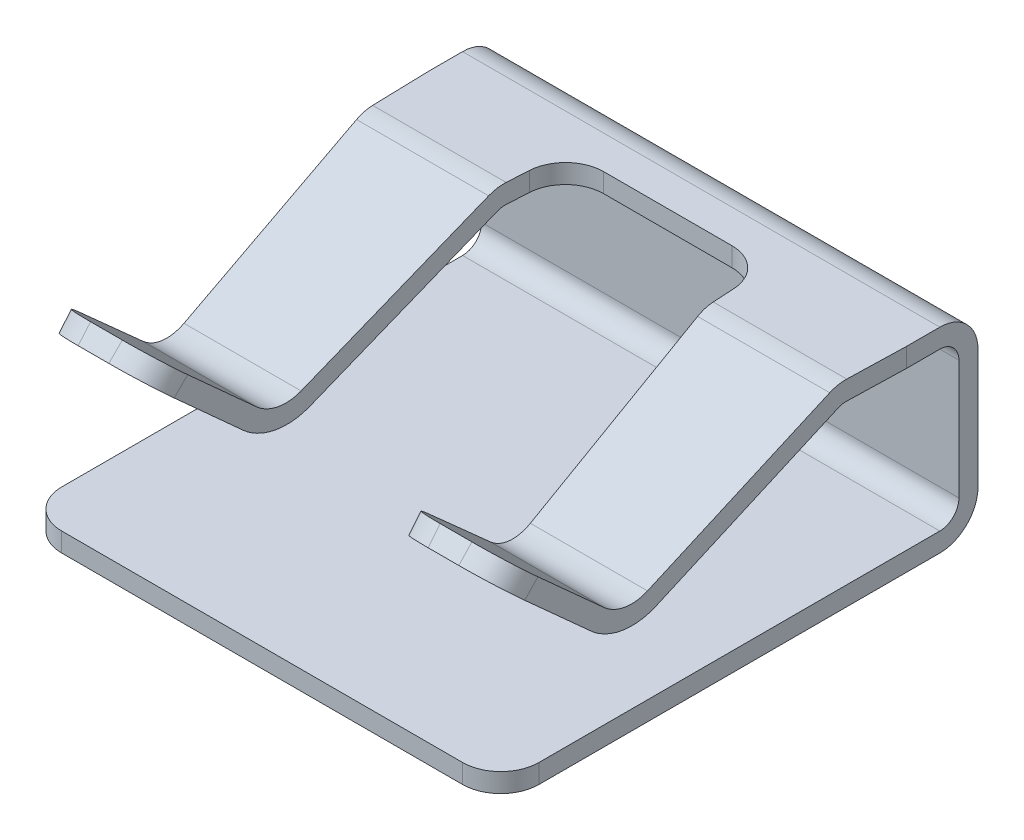
SolidWorks part; units mm, degrees
ref_plane "Front Plane" through (0, 0, 0) normal (0, 0, 1) x (1, 0, 0)
ref_plane "Top Plane" through (0, 0, 0) normal (0, 1, 0) x (1, 0, 0)
ref_plane "Right Plane" through (0, 0, 0) normal (1, 0, 0) x (0, 0, -1)
sketch "Sketch1" plane through (0, 0, 0) normal (1, 0, 0) x (0, 0, -1)
  line L0 (0, 0.4) -> (0, 1.65)
  line L1 (-0.4, 2.05) -> (-1.3588, 2.05)
  line L2 (-1.5322, 2.0105) -> (-3.3908, 1.1162)
  line L3 (-3.8317, 1.1793) -> (-4.8, 2.05)
  line L4 (-0.4, 0) -> (-5, 0)
  line L5 (-0.4, 0.2) -> (-5, 0.2)
  line L6 (-0.2, 0.4) -> (-0.2, 1.65)
  line L7 (-0.4, 1.85) -> (-1.3588, 1.85)
  line L8 (-1.4455, 1.8302) -> (-3.3041, 0.936)
  line L9 (-3.9655, 1.0305) -> (-4.9337, 1.9013)
  line L10 (-4.9337, 1.9013) -> (-4.8, 2.05)
  line L11 (-5, 0.2) -> (-5, 0)
  arc A0 (0, 0.4) -> (-0.4, 0) centre (-0.4, 0.4) cw
  arc A1 (0, 1.65) -> (-0.4, 2.05) centre (-0.4, 1.65) ccw
  arc A2 (-3.3908, 1.1162) -> (-3.8317, 1.1793) centre (-3.5643, 1.4767) cw
  arc A3 (-1.3588, 2.05) -> (-1.5322, 2.0105) centre (-1.3588, 1.65) ccw
  arc A4 (-0.2, 0.4) -> (-0.4, 0.2) centre (-0.4, 0.4) cw
  arc A5 (-0.2, 1.65) -> (-0.4, 1.85) centre (-0.4, 1.65) ccw
  arc A6 (-1.3588, 1.85) -> (-1.4455, 1.8302) centre (-1.3588, 1.65) ccw
  arc A7 (-3.3041, 0.936) -> (-3.9655, 1.0305) centre (-3.5643, 1.4767) cw
  point P12 (0, 0)
  point P17 (-3.6324, 1)
  point P20 (-1.45, 2.05)
  dimension "D6" = 0.4
  dimension "D7" = 0.4
  dimension "D1" = 2.05
  dimension "D2" = 5
  dimension "D3" = 1.45
  dimension "D4" = 1
  dimension "D5" = 0.2
  dimension "D8" = 0.2
extrude "Boss-Extrude1" add sketch "Sketch1" along normal mid plane 5
sketch "Sketch2" plane through (0, 2.05, 0) normal (0, 1, 0) x (1, 0, 0)
  line L0 (0, 0) -> (0, -4.8) construction
  line L1 (2.5, -4.8) -> (-2.5, -4.8) construction
  line L2 (-1.05, -0.75) -> (1.05, -0.75)
  line L3 (2.5, -5) -> (-2.5, -5) construction
  line L4 (-1.05, -0.75) -> (-1.289, -4.9337)
  line L5 (2.5, -4.9337) -> (-2.5, -4.9337) construction
  line L6 (1.05, -0.75) -> (1.289, -4.9337)
  line L7 (-1.289, -4.9337) -> (1.289, -4.9337)
  line L8 (-2.5, -0.75) -> (-2.5, -4.9337)
  line L9 (-2.5, -0.4) -> (-2.5, -1.3588) construction
  line L10 (-2.5, -4.9337) -> (-2.3861, -4.9337)
  line L11 (-2.3861, -4.9337) -> (-2.5, -0.75)
  line L12 (2.5, -4.9337) -> (2.3861, -4.9337)
  line L13 (2.5, -0.75) -> (2.5, -4.9337)
  line L14 (2.3861, -4.9337) -> (2.5, -0.75)
  point P8 (0, -0.75)
  point P23 (-2.3861, -4.9337)
  dimension "D1" = 4.25
  dimension "D2" = 2.1
extrude "Cut-Extrude1" cut sketch "Sketch2" against normal blind 1.5
fillet "Fillet1" radius 0.4 8 edges at (2.3879, 1.9756, 4.8669) (1.2852, 1.9756, 4.8669) (-1.2852, 1.9756, 4.8669) (-2.3879, 1.9756, 4.8669) (1.05, 1.95, 0.75) (-1.05, 1.95, 0.75) (2.5, 0.1, 5) (-2.5, 0.1, 5)
